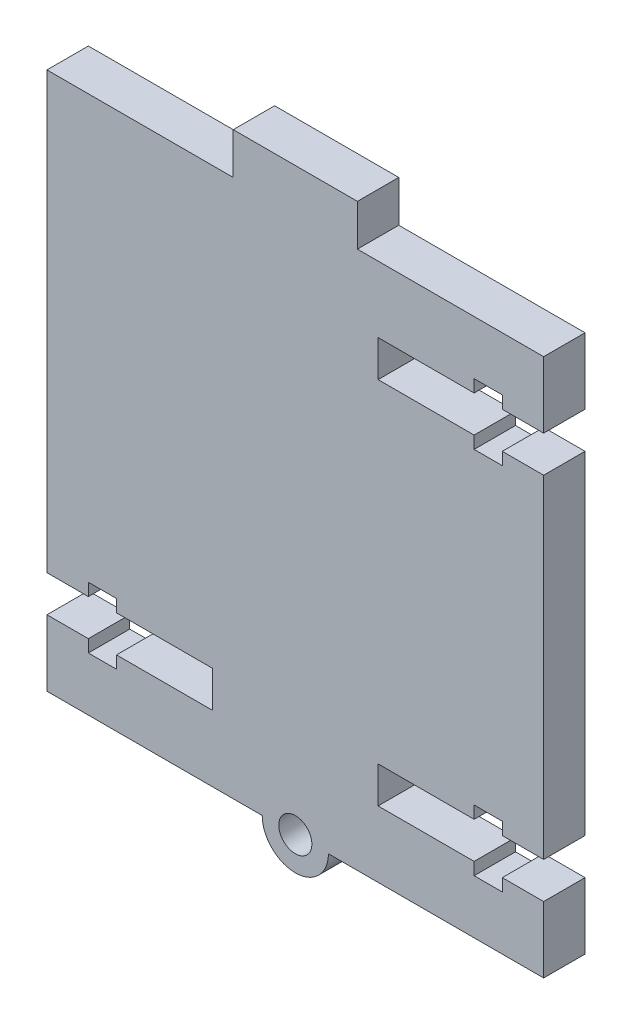
SolidWorks part; units mm, degrees
ref_plane "Front Plane" through (0, 0, 0) normal (0, 0, 1) x (1, 0, 0)
ref_plane "Top Plane" through (0, 0, 0) normal (0, 1, 0) x (1, 0, 0)
ref_plane "Right Plane" through (0, 0, 0) normal (1, 0, 0) x (0, 0, -1)
sketch "Sketch1" plane through (0, 0, 0) normal (0, 0, 1) x (1, 0, 0)
  line L0 (7.5, 32.5) -> (7.5, 37.5)
  line L1 (-30, 32.5) -> (-7.5, 32.5)
  line L2 (-30, 32.5) -> (-30, -32.5)
  line L3 (-30, -32.5) -> (30, -32.5)
  line L4 (30, 32.5) -> (30, -32.5)
  line L5 (7.5, 37.5) -> (-7.5, 37.5)
  line L6 (-7.5, 37.5) -> (-7.5, 32.5)
  line L7 (7.5, 32.5) -> (30, 32.5)
  dimension "D1" = 60
  dimension "D2" = 65
  dimension "D3" = 30
  dimension "D4" = 32.5
  dimension "D5" = 15
  dimension "D6" = 22.5
  dimension "D7" = 5
extrude "Boss-Extrude1" add sketch "Sketch1" along normal blind 5
sketch "Sketch3" plane through (0, 0, 5) normal (0, 0, 1) x (1, 0, 0)
  line L0 (0, 0) -> (28.1265, 0) construction
  line L13 (30, -32.5) -> (30, 32.5) construction
  line L14 (30, 24.5) -> (25, 24.5)
  line L15 (25, 24.5) -> (25, 26)
  line L16 (25, 26) -> (21.6, 26)
  line L17 (21.6, 26) -> (21.6, 24.5)
  line L18 (21.6, 24.5) -> (10, 24.5)
  line L19 (10, 24.5) -> (10, 20.1)
  line L20 (10, 20.1) -> (21.6, 20.1)
  line L21 (21.6, 20.1) -> (21.6, 18.6)
  line L22 (21.6, 18.6) -> (25, 18.6)
  line L23 (25, 18.6) -> (25, 20.1)
  line L24 (25, 20.1) -> (30, 20.1)
  line L25 (30, 24.5) -> (30, 20.1)
  line L26 (-7.5, 32.5) -> (-30, 32.5) construction
  line L27 (0, 0) -> (0, 42.4523) construction
  line L28 (30, -24.5) -> (30, -20.1)
  line L29 (25, -20.1) -> (30, -20.1)
  line L30 (25, -18.6) -> (25, -20.1)
  line L31 (21.6, -18.6) -> (25, -18.6)
  line L32 (21.6, -20.1) -> (21.6, -18.6)
  line L33 (10, -20.1) -> (21.6, -20.1)
  line L34 (10, -24.5) -> (10, -20.1)
  line L35 (21.6, -24.5) -> (10, -24.5)
  line L36 (21.6, -26) -> (21.6, -24.5)
  line L37 (25, -26) -> (21.6, -26)
  line L38 (25, -24.5) -> (25, -26)
  line L39 (30, -24.5) -> (25, -24.5)
  line L40 (-30, -24.5) -> (-25, -24.5)
  line L41 (-25, -24.5) -> (-25, -26)
  line L42 (-25, -26) -> (-21.6, -26)
  line L43 (-21.6, -26) -> (-21.6, -24.5)
  line L44 (-21.6, -24.5) -> (-10, -24.5)
  line L45 (-10, -24.5) -> (-10, -20.1)
  line L46 (-10, -20.1) -> (-21.6, -20.1)
  line L47 (-21.6, -20.1) -> (-21.6, -18.6)
  line L48 (-21.6, -18.6) -> (-25, -18.6)
  line L49 (-25, -18.6) -> (-25, -20.1)
  line L50 (-25, -20.1) -> (-30, -20.1)
  line L51 (-30, -24.5) -> (-30, -20.1)
  dimension "D8" = 4.4
  dimension "D9" = 1.5
  dimension "D10" = 1.5
  dimension "D11" = 3.4
  dimension "D12" = 5
  dimension "D13" = 8
  dimension "D14" = 20
extrude "Cut-Extrude1" cut sketch "Sketch3" against normal blind 5
sketch "Sketch5" plane through (0, 0, 5) normal (0, 0, 1) x (1, 0, 0)
  line L0 (0, 0) -> (0, -42.6845) construction
  line L1 (-30, -32.5) -> (30, -32.5) construction
  circle A0 centre (0, -32.5) radius 2
  circle A1 centre (0, -32.5) radius 4
  dimension "D1" = 4
  dimension "D2" = 8
extrude "Boss-Extrude2" add sketch "Sketch5" against normal blind 5
sketch "Sketch6" plane through (0, 0, 5) normal (0, 0, 1) x (1, 0, 0)
  line L0 (-2, -32.5) -> (2, -32.5) construction
  circle A0 centre (0, -32.5) radius 2
  dimension "D1" = 4
extrude "Cut-Extrude2" cut sketch "Sketch6" against normal blind 5
